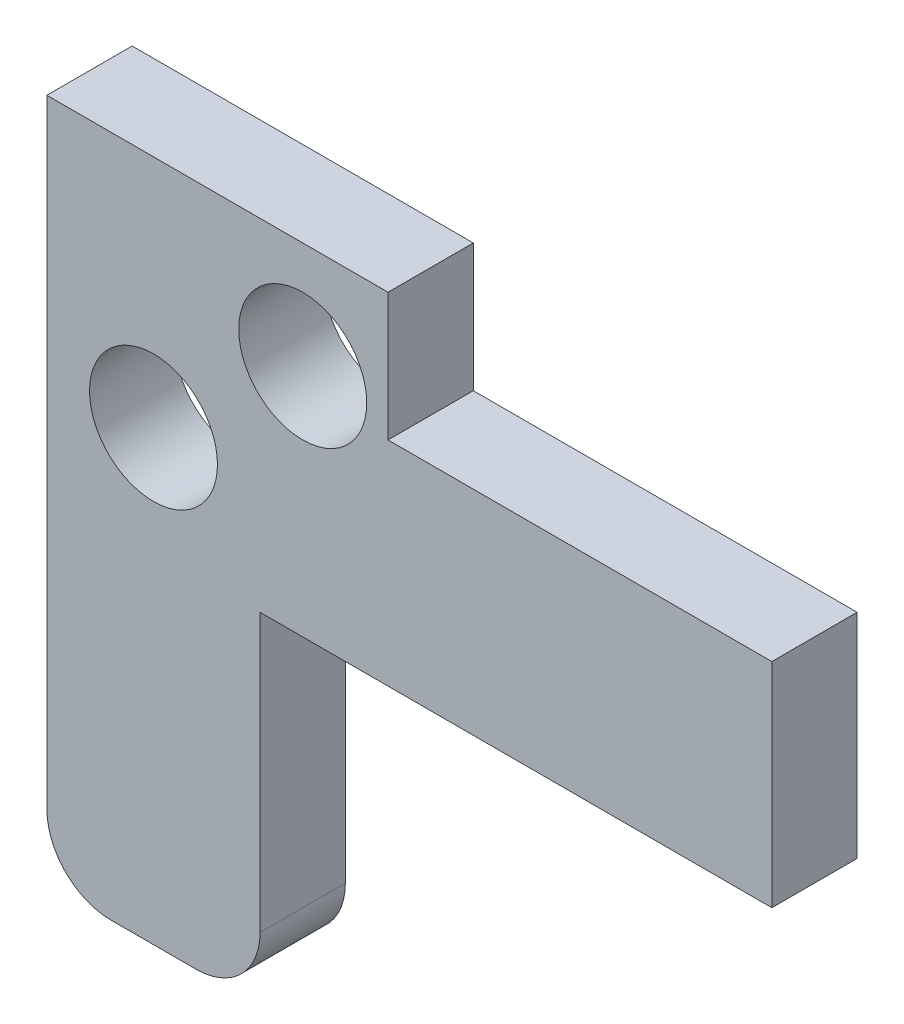
SolidWorks part; units mm, degrees
ref_plane "前视基准面" through (0, 0, 0) normal (0, 0, 1) x (1, 0, 0)
ref_plane "上视基准面" through (0, 0, 0) normal (0, 1, 0) x (1, 0, 0)
ref_plane "右视基准面" through (0, 0, 0) normal (1, 0, 0) x (0, 0, -1)
sketch "草图1" plane through (0, 0, 0) normal (0, 0, 1) x (1, 0, 0)
  line L0 (0, 0) -> (0, 15)
  dimension "D1" = 15
sketch "草图6" plane through (0, 0, 0) normal (0, 0, 1) x (1, 0, 0)
  line L1 (0, 0) -> (-5, 0)
  line L2 (0, 0) -> (0, 21)
  line L3 (0, 21) -> (-5, 21)
  line L4 (-5, 0) -> (-5, 21)
  dimension "D1" = 21
  dimension "D2" = 5
extrude "凸台-拉伸1" add sketch "草图6" along normal blind 2
sketch "草图10" plane through (0, 0, 0) normal (1, 0, 0) x (0, 0, -1)
  line L0 (0, 0) -> (0, 21) construction
  line L1 (0, 21) -> (-2, 21)
  line L2 (0, 21) -> (0, 16)
  line L3 (0, 16) -> (-2, 16)
  line L4 (-2, 21) -> (-2, 16)
  line L5 (-2, 0) -> (-2, 21) construction
  line L6 (-2, 21) -> (0, 21) construction
  dimension "D1" = 5
  dimension "D2" = 0
extrude "凸台-拉伸3" add sketch "草图10" along normal blind 20
sketch "草图11" plane through (0, 0, 0) normal (0, 0, -1) x (-1, 0, 0)
  line L0 (-20, 21) -> (5, 21) construction
  line L1 (-20, 16) -> (-12, 16)
  line L2 (-20, 16) -> (-20, 21)
  line L3 (-20, 21) -> (-12, 21)
  line L4 (-12, 16) -> (-12, 21)
  dimension "D1" = 8
extrude "切除-拉伸3" cut sketch "草图11" against normal blind 20
sketch "草图12" plane through (0, 0, 0) normal (0, 0, -1) x (-1, 0, 0)
  line L0 (0, 16) -> (5, 16) construction
  line L1 (5, 21) -> (5, 0) construction
  line L2 (5, 16) -> (5, 21) construction
  line L3 (5, 21) -> (5, 18.5) construction
  line L4 (5, 18.5) -> (0, 18.5) construction
  line L5 (0, 18.5) -> (2.5, 18.5) construction
  circle A0 centre (2.5, 18.5) radius 1.5
  dimension "D1" = 3
extrude "切除-拉伸4" cut sketch "草图12" against normal blind 20
sketch "草图13" plane through (0, 0, 0) normal (0, -1, 0) x (1, 0, 0)
  line L1 (0, 2) -> (-5, 2)
  line L2 (0, 2) -> (0, 0)
  line L3 (0, 0) -> (-5, 0)
  line L4 (-5, 2) -> (-5, 0)
extrude "切除-拉伸5" cut sketch "草图13" against normal blind 8
fillet "圆角1" radius 1.5 2 edges at (-5, 8, 1) (0, 8, 1)
sketch "草图19" plane through (0, 21, 0) normal (0, 1, 0) x (1, 0, 0)
  line L0 (12, -2) -> (-5, -2) construction
  line L1 (-5, 0) -> (3, 0)
  line L2 (-5, 0) -> (-5, -2)
  line L3 (-5, -2) -> (3, -2)
  line L4 (3, 0) -> (3, -2)
  dimension "D1" = 8
extrude "凸台-拉伸6" add sketch "草图19" along normal blind 3
sketch "草图20" plane through (0, 0, 0) normal (0, 0, -1) x (-1, 0, 0)
  line L0 (-3, 24) -> (5, 24) construction
  line L1 (5, 24) -> (5, 9.5) construction
  circle A0 centre (-1, 21.5) radius 1.5
  dimension "D1" = 3
  dimension "D2" = 2.5
  dimension "D3" = 6
extrude "切除-拉伸7" cut sketch "草图20" against normal blind 5
